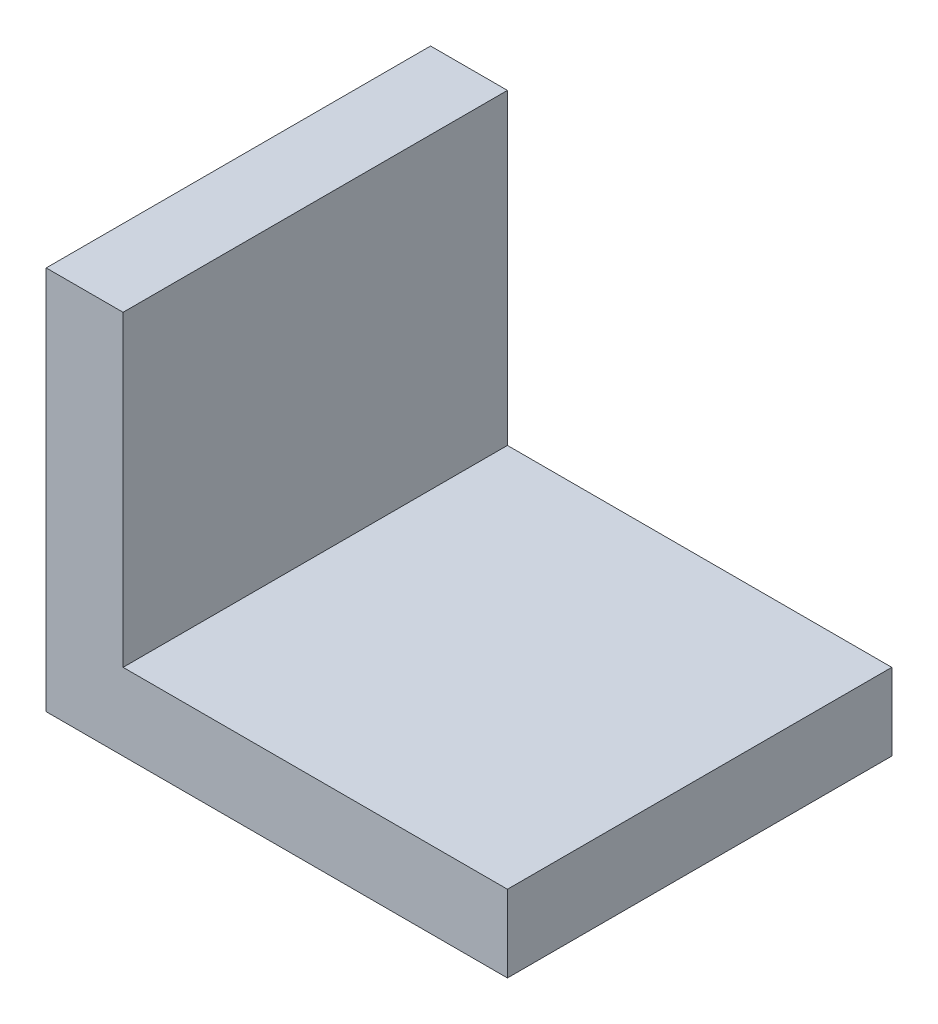
SolidWorks part; units mm, degrees
ref_plane "Front Plane" through (0, 0, 0) normal (0, 0, 1) x (1, 0, 0)
ref_plane "Top Plane" through (0, 0, 0) normal (0, 1, 0) x (1, 0, 0)
ref_plane "Right Plane" through (0, 0, 0) normal (1, 0, 0) x (0, 0, -1)
sketch "Sketch1" plane through (0, 0, 0) normal (0, 1, 0) x (1, 0, 0)
  line L1 (-6, 5) -> (6, 5)
  line L2 (-6, 5) -> (-6, -5)
  line L3 (-6, -5) -> (6, -5)
  line L4 (6, 5) -> (6, -5)
  line L5 (-6, 5) -> (6, -5) construction
  line L6 (-6, -5) -> (6, 5) construction
  point P0 (0, 0)
  dimension "D1" = 10
  dimension "D2" = 12
extrude "Boss-Extrude1" add sketch "Sketch1" along normal blind 2
sketch "Sketch2" plane through (0, 2, 0) normal (0, 1, 0) x (1, 0, 0)
  line L0 (-6, -5) -> (6, -5) construction
  line L1 (-6, 5) -> (-4, 5)
  line L2 (-6, 5) -> (-6, -5)
  line L3 (-6, -5) -> (-4, -5)
  line L4 (-4, 5) -> (-4, -5)
  dimension "D1" = 2
extrude "Boss-Extrude2" add sketch "Sketch2" along normal blind 8
